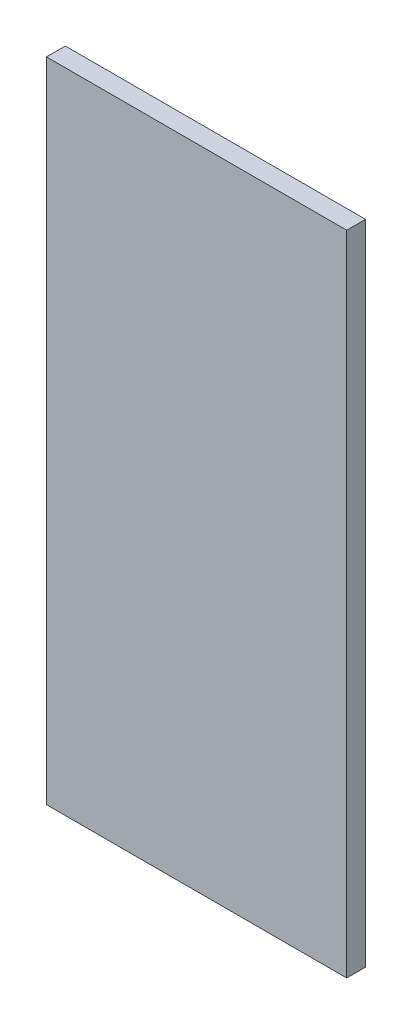
SolidWorks part; units mm, degrees
ref_plane "Front Plane" through (0, 0, 0) normal (0, 0, 1) x (1, 0, 0)
ref_plane "Top Plane" through (0, 0, 0) normal (0, 1, 0) x (1, 0, 0)
ref_plane "Right Plane" through (0, 0, 0) normal (1, 0, 0) x (0, 0, -1)
sketch "Sketch1" plane through (0, 0, 0) normal (0, 0, 1) x (1, 0, 0)
  line L1 (-127.5, 275) -> (127.5, 275)
  line L2 (-127.5, 275) -> (-127.5, -275)
  line L3 (-127.5, -275) -> (127.5, -275)
  line L4 (127.5, 275) -> (127.5, -275)
  point P4 (127.5, 0)
  point P5 (0, -275)
  dimension "D1" = 550
  dimension "D2" = 255
extrude "Boss-Extrude1" add sketch "Sketch1" along normal blind 16 contours L2 L3 L4 L1
equation "\"Length\"= 45cm"
equation "\"Width\"= 16cm"
equation "\"Curvature radius\"= 13mm"
equation "\"Extra\"= 5cm"
equation "\"D1@Sketch1\"=\"Length\"+\"Extra\"*2"
